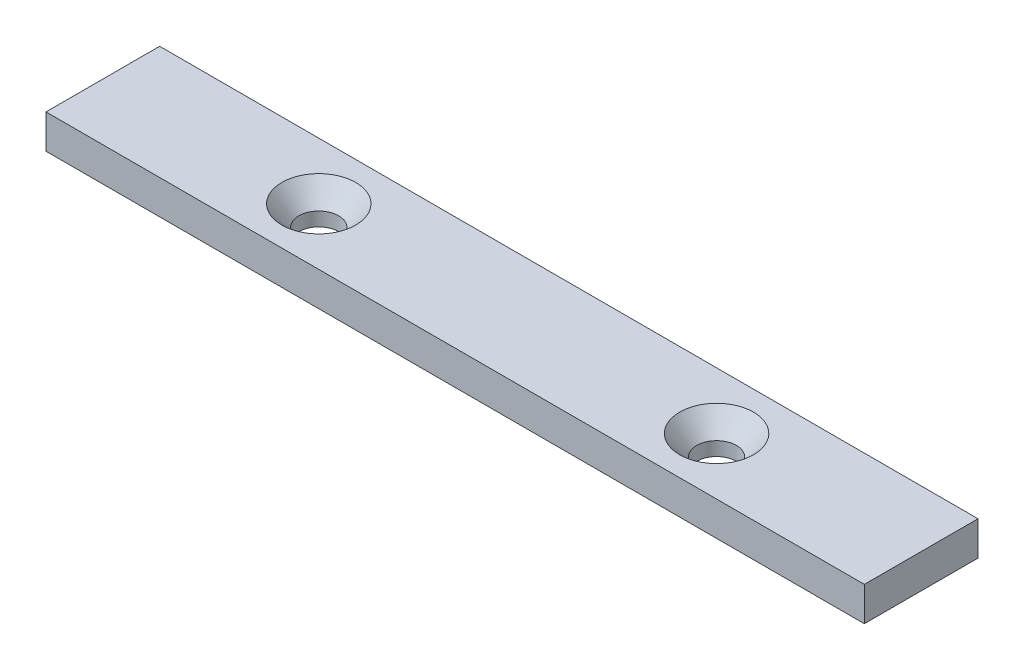
SolidWorks part; units mm, degrees
ref_plane "Front Plane" through (0, 0, 0) normal (0, 0, 1) x (1, 0, 0)
ref_plane "Top Plane" through (0, 0, 0) normal (0, 1, 0) x (1, 0, 0)
ref_plane "Right Plane" through (0, 0, 0) normal (1, 0, 0) x (0, 0, -1)
sketch "Sketch1" plane through (0, 0, 0) normal (0, 1, 0) x (1, 0, 0)
  line L1 (0, 0) -> (144, 0)
  line L2 (0, 0) -> (0, 20)
  line L3 (0, 20) -> (144, 20)
  line L4 (144, 0) -> (144, 20)
  dimension "D1" = 20
  dimension "D2" = 144
extrude "Boss-Extrude1" add sketch "Sketch1" along normal blind 6
hole_wizard "CSK for M5 Flat Head Machine Screw1" positions "3DSketch1" profile "Sketch2" countersink size "M5" standard "ANSI Metric" end condition through all
sketch3d "3DSketch1"
  line L0 (0, 6, 0) -> (144, 6, 0) construction
  line L1 (0, 6, -20) -> (0, 6, 0) construction
  point P0 (38, 6, -10)
  point P2 (108, 6, -10)
  dimension "D1" = 10
  dimension "D2" = 10
  dimension "D3" = 38
  dimension "D4" = 70
sketch "Sketch2" plane through (38, 6, -10) normal (1, 0, 0) x (0, 0, 1)
  line L0 (0, 0) -> (0, 6)
  line L1 (0, 6) -> (3.5, 6)
  line L2 (3.5, 6) -> (3.5, 3.5753)
  line L3 (3.5, 3.5753) -> (6.5, 0)
  line L5 (6.5, 0) -> (0, 0)
  line L6 (-3.5, 3.5753) -> (-6.5, 0) construction
  line L11 (0, -6.35) -> (0, 107.95) construction
  dimension "Thru Hole Dia." = 7
  dimension "Thru Hole Depth" = 6
  dimension "Near C'Sink Dia." = 13
  dimension "Near C'Sink Angle" = 80
